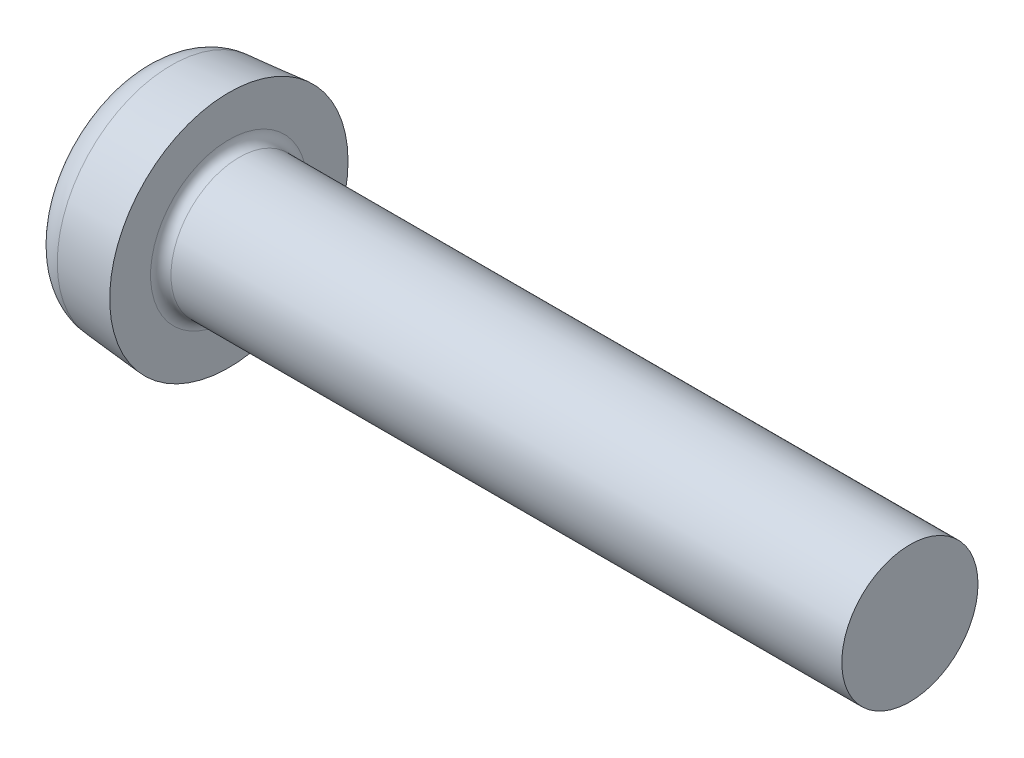
SolidWorks part; units mm, degrees
ref_plane "Front" through (0, 0, 0) normal (0, 0, 1) x (1, 0, 0)
ref_plane "Top" through (0, 0, 0) normal (0, 1, 0) x (1, 0, 0)
ref_plane "Right" through (0, 0, 0) normal (1, 0, 0) x (0, 0, -1)
sketch "Sketch1" plane through (0, 0, 0) normal (0, 0, 1) x (1, 0, 0)
  line L0 (22.6, 2) -> (4, 2)
  line L1 (2.6, 2.3) -> (2.6, 3.5)
  line L2 (2.6, 3.5) -> (0, 3.2725)
  line L3 (4, 2) -> (2.9, 2)
  line L4 (22.6, 2) -> (22.6, 0)
  line L5 (4.5158, 0) -> (-13.5157, 0) construction
  line L6 (22.6, 0) -> (0, 0)
  line L7 (0, 0) -> (0, 3.2725)
  arc A1 (2.6, 2.3) -> (2.9, 2) centre (2.9, 2.3) ccw
  dimension "d" = 4
  dimension "r" = 0.3
  dimension "l" = 20
  dimension "a" = 1.4
  dimension "D2" = 95
  dimension "k" = 2.6
  dimension "dk" = 7
revolve "Base" add sketch "Sketch1" angle 360 about L5
cosmetic thread "ThreadCosmetic1" [suppressed] parameters "bb"=20
sketch "Sketch6" plane through (0, 0, 0) normal (1, 0, 0) x (0, 0, -1)
  line L0 (-1.9271, 0) -> (2.0512, 0) construction
  line L1 (0, 1.8651) -> (0, -2.0207) construction
  line L2 (0.41, 0.41) -> (0.41, 2.05)
  line L3 (0.41, 2.05) -> (-0.41, 2.05)
  line L4 (-0.41, 0.41) -> (-0.41, 2.05)
  line L5 (0.41, 0.41) -> (2.05, 0.41)
  line L6 (2.05, 0.41) -> (2.05, -0.41)
  line L7 (-2.05, 0.41) -> (-2.05, -0.41)
  line L8 (-0.41, 0.41) -> (-2.05, 0.41)
  line L9 (-0.41, -0.41) -> (-2.05, -0.41)
  line L10 (0.41, -0.41) -> (2.05, -0.41)
  line L11 (-0.41, -0.41) -> (-0.41, -2.05)
  line L12 (0.41, -2.05) -> (-0.41, -2.05)
  line L13 (0.41, -0.41) -> (0.41, -2.05)
  point P16 (-2.05, 0)
  point P17 (2.05, 0)
extrude "CrossRecess" cut sketch "Sketch6" along normal blind 2.6
fillet "Fillet5" radius 0.3 4 edges at (1.3, -0.41, 0.41) (1.3, -0.41, -0.41) (1.3, 0.41, 0.41) (1.3, 0.41, -0.41)
sketch "Sketch8" [suppressed] plane through (0, 0, 0) normal (0, 0, 1) x (1, 0, 0)
  line L0 (12, 4) -> (8.2, 3.5)
  line L1 (8.2, 3.5) -> (5, 3.5)
  line L3 (50, -4) -> (50, 4) construction
  line L4 (5, -6.5) -> (5, 6.5) construction
  line L6 (5, 3.5) -> (5, 14)
  line L7 (5, 14) -> (12, 14)
  line L8 (12, 14) -> (12, 4)
  line L9 (52.4753, 0) -> (42.9594, 0) construction
  dimension "x" = 1.75
  dimension "THD_MINOR" = 3.242
  dimension "d" = 4
  dimension "D1" = 24
  dimension "b" = 38
fillet "HeadFillet" radius 1 1 edges at (0, 0, -3.2725)
draft "Draft1" type of draft neutral plane draft angle 20 faces to draft 4 face at (1.3, 0, 2.05) face at (1.3, -2.05, 0) face at (1.3, 0, -2.05) face at (1.3, 2.05, 0) neutral plane through (0, 0, 0) neutral plane normal (-1, 0, 0) parameters "D1"=20
sketch "Sketch7" plane through (0, 0, 0) normal (1, 0, 0) x (0, 0, -1)
  line L0 (-8.3217, 0) -> (7.4212, 0) construction
  line L1 (0, 7.4989) -> (0, -7.9646) construction
  line L2 (0, 0) -> (6.8599, 6.8599) construction
  line L3 (1.4496, 1.4496) -> (0, 0.7736)
  line L4 (0, 0) -> (-6.8599, 6.8599) construction
  line L5 (1.4496, 1.4496) -> (0.7736, 0)
  line L6 (1.4496, -1.4496) -> (0, -0.7736)
  line L7 (1.4496, -1.4496) -> (0.7736, 0)
  line L8 (-1.4496, -1.4496) -> (0, -0.7736)
  line L9 (-1.4496, -1.4496) -> (-0.7736, 0)
  line L10 (-1.4496, 1.4496) -> (0, 0.7736)
  line L11 (-1.4496, 1.4496) -> (-0.7736, 0)
  dimension "D2" = 20
  dimension "m" = 4.1
extrude "Cut-Extrude3" [suppressed] cut sketch "Sketch7" along normal blind 10 draft 20
sketch "Sketch10" plane through (0, 0, 0) normal (0, 0, 1) x (1, 0, 0)
  line L0 (22.6, 1.6718) -> (22.7895, 2)
  line L1 (22.7895, 2) -> (22.7895, 2.379)
  line L2 (22.7895, 2.379) -> (22.4105, 2.379)
  line L3 (22.4105, 2.379) -> (22.4105, 2)
  line L4 (22.4105, 2) -> (22.6, 1.6718)
  line L5 (22.6, 2) -> (4, 2) construction
  line L6 (22.6, 2) -> (22.6, 0) construction
  line L7 (0, 0) -> (57.111, 0) construction
  dimension "D1" = 0.379
revolve "Cut-Revolve10" [suppressed] cut sketch "Sketch10" angle 360 about L7
pattern_linear "LPattern10" [suppressed] count 44 spacing 0.4548 along (1, 0, 0)
equation "\"D1@Sketch6\" = \"m@Sketch6\" / 5"
equation "\"D1@Sketch8\" = \"d@Sketch8\" + 20"
equation "\"D1@Sketch10\" =  ( \"d@Sketch1\" - \"THD_MINOR@ThreadCosmetic1\" )  / 2"
equation "\"D3@LPattern10\" = \"D1@Sketch10\" * 1.2"
equation "\"D1@LPattern10\" = \"bb@ThreadCosmetic1\" / \"D3@LPattern10\" "
